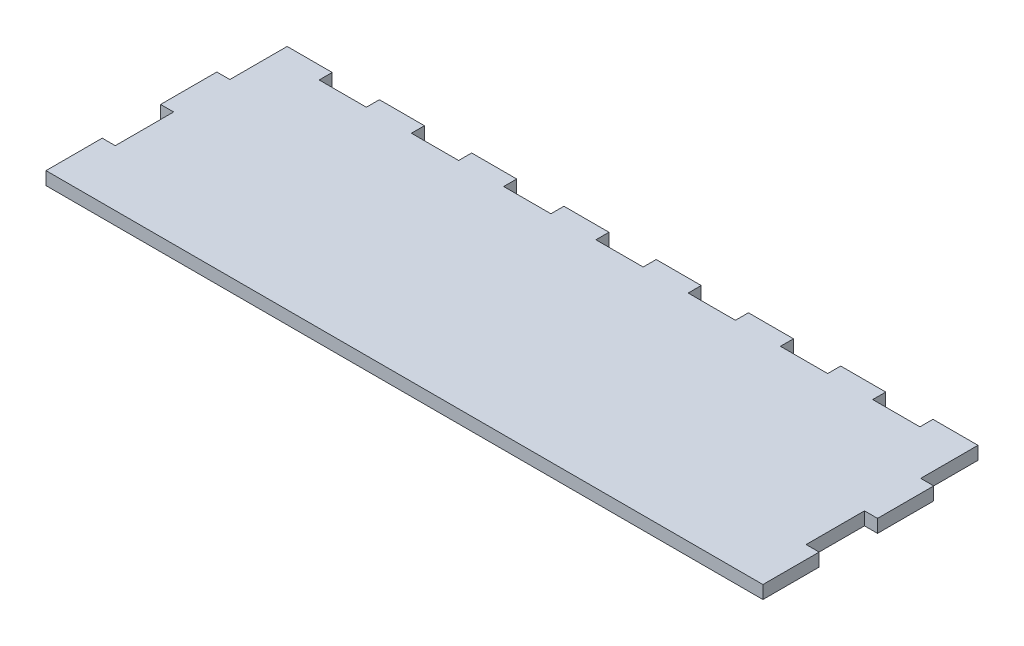
SolidWorks part; units mm, degrees
material "Plywood"
ref_plane "Front Plane" through (0, 0, 0) normal (0, 0, 1) x (1, 0, 0)
ref_plane "Top Plane" through (0, 0, 0) normal (0, 1, 0) x (1, 0, 0)
ref_plane "Right Plane" through (0, 0, 0) normal (1, 0, 0) x (0, 0, -1)
ref_plane "Plane1" through (0, 0, 0) normal (0, -1, 0) x (1, 0, 0)
sketch "Sketch1" plane through (0, 0, 0) normal (0, -1, 0) x (1, 0, 0)
  line L0 (48.4667, 6) -> (48.4667, 0)
  line L1 (48.4667, 0) -> (69.2, 0)
  line L2 (69.2, 0) -> (69.2, 6)
  line L3 (69.2, 6) -> (90.9333, 6)
  line L4 (90.9333, 6) -> (90.9333, 0)
  line L5 (90.9333, 0) -> (111.6667, 0)
  line L6 (111.6667, 0) -> (111.6667, 6)
  line L7 (111.6667, 6) -> (133.4, 6)
  line L8 (133.4, 6) -> (133.4, 0)
  line L9 (133.4, 0) -> (154.1333, 0)
  line L10 (154.1333, 0) -> (154.1333, 6)
  line L11 (154.1333, 6) -> (175.8667, 6)
  line L12 (175.8667, 6) -> (175.8667, 0)
  line L13 (175.8667, 0) -> (196.6, 0)
  line L14 (196.6, 0) -> (196.6, 6)
  line L15 (196.6, 6) -> (218.3333, 6)
  line L16 (218.3333, 6) -> (218.3333, 0)
  line L17 (218.3333, 0) -> (239.0667, 0)
  line L18 (239.0667, 0) -> (239.0667, 6)
  line L19 (239.0667, 6) -> (260.8, 6)
  line L20 (260.8, 6) -> (260.8, 0)
  line L21 (260.8, 0) -> (281.5333, 0)
  line L22 (281.5333, 0) -> (281.5333, 6)
  line L23 (281.5333, 6) -> (303.2667, 6)
  line L24 (303.2667, 6) -> (303.2667, 0)
  line L25 (303.2667, 0) -> (324, 0)
  line L26 (324, 0) -> (324, 26.375)
  line L27 (324, 26.375) -> (330, 26.375)
  line L28 (330, 26.375) -> (330, 52.25)
  line L29 (330, 52.25) -> (324, 52.25)
  line L30 (324, 52.25) -> (324, 79.125)
  line L31 (324, 79.125) -> (330, 79.125)
  line L32 (330, 79.125) -> (330, 105)
  line L33 (330, 105) -> (0, 105)
  line L34 (0, 105) -> (0, 79.125)
  line L35 (0, 79.125) -> (6, 79.125)
  line L36 (6, 79.125) -> (6, 52.25)
  line L37 (6, 52.25) -> (0, 52.25)
  line L38 (0, 52.25) -> (0, 26.375)
  line L39 (0, 26.375) -> (6, 26.375)
  line L40 (6, 26.375) -> (6, 0)
  line L41 (6, 0) -> (26.7333, 0)
  line L42 (26.7333, 0) -> (26.7333, 6)
  line L43 (26.7333, 6) -> (48.4667, 6)
extrude "Boss-Extrude1" add sketch "Sketch1" against normal blind 6
